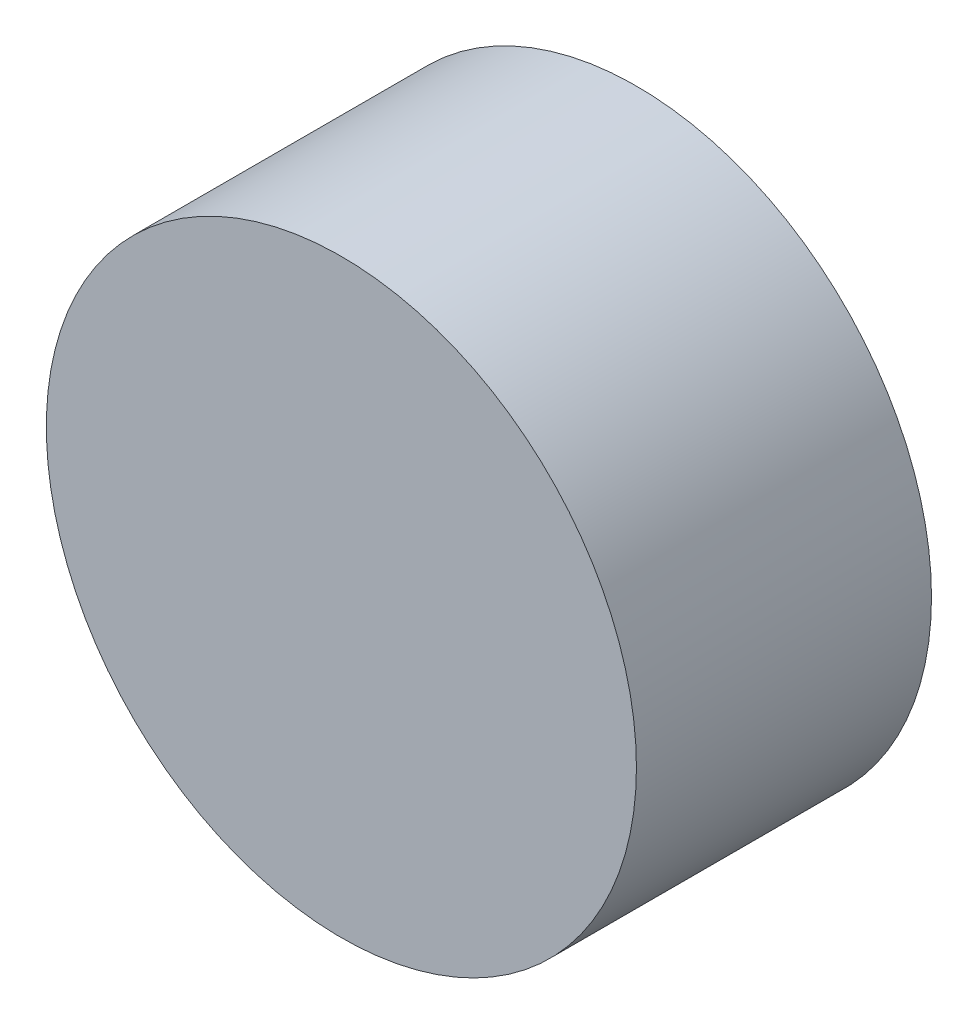
SolidWorks part; units mm, degrees
ref_plane "Front Plane" through (0, 0, 0) normal (0, 0, 1) x (1, 0, 0)
ref_plane "Top Plane" through (0, 0, 0) normal (0, 1, 0) x (1, 0, 0)
ref_plane "Right Plane" through (0, 0, 0) normal (1, 0, 0) x (0, 0, -1)
sketch "Sketch1" plane through (0, 0, 0) normal (0, 0, 1) x (1, 0, 0)
  circle A0 centre (0, 0) radius 8.89
  dimension "D1" = 17.78
extrude "Boss-Extrude1" add sketch "Sketch1" along normal blind 8.89
